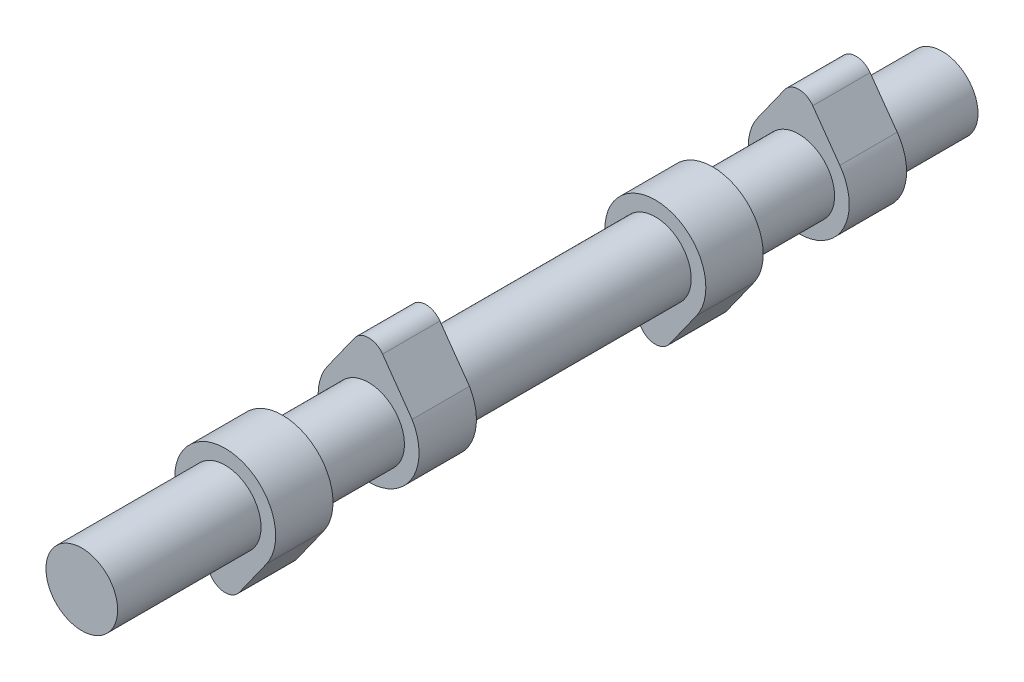
SolidWorks part; units mm, degrees
ref_plane "Front Plane" through (0, 0, 0) normal (0, 0, 1) x (1, 0, 0)
ref_plane "Top Plane" through (0, 0, 0) normal (0, 1, 0) x (1, 0, 0)
ref_plane "Right Plane" through (0, 0, 0) normal (1, 0, 0) x (0, 0, -1)
sketch "Sketch1" plane through (0, 0, 0) normal (0, 0, 1) x (1, 0, 0)
  circle A0 centre (0, 0) radius 6.25
  dimension "D1" = 12.5
extrude "Boss-Extrude1" add sketch "Sketch1" along normal blind 125
ref_plane "Plane1" through (0, 0, 15) normal (0, 0, -1) x (-1, 0, 0)
sketch "Sketch3" plane through (0, 0, 15) normal (0, 0, -1) x (-1, 0, 0)
  line L1 (-2.4438, 11.74) -> (-7.1686, 5.104)
  line L2 (2.4438, 11.74) -> (7.1686, 5.104)
  circle A0 centre (0, 0) radius 6.25
  arc A1 (-7.1686, 5.104) -> (7.1686, 5.104) centre (0, 0) ccw
  arc A2 (2.4438, 11.74) -> (-2.4438, 11.74) centre (0, 10) ccw
extrude "Boss-Extrude2" add sketch "Sketch3" against normal blind 10
ref_plane "Plane2" through (0, 0, 40) normal (0, 0, -1) x (-1, 0, 0)
ref_plane "Plane3" through (0, 0, 15) normal (0, 0, -1) x (-1, 0, 0)
sketch "Sketch6" plane through (0, 0, 40) normal (0, 0, -1) x (-1, 0, 0)
  line L1 (-2.4438, -11.74) -> (-7.1686, -5.104)
  line L2 (2.4438, -11.74) -> (7.1686, -5.104)
  circle A0 centre (0, 0) radius 6.25
  arc A1 (7.1686, -5.104) -> (-7.1686, -5.104) centre (0, 0) ccw
  arc A2 (-2.4438, -11.74) -> (2.4438, -11.74) centre (0, -10) ccw
extrude "Boss-Extrude3" add sketch "Sketch6" against normal blind 10
ref_plane "Plane4" through (0, 0, 90) normal (0, 0, -1) x (-1, 0, 0)
sketch "Sketch7" plane through (0, 0, 40) normal (0, 0, -1) x (-1, 0, 0)
  line L2 (2.4438, -11.74) -> (7.1686, -5.104)
  line L3 (-7.1686, -5.104) -> (-2.4438, -11.74)
  line L4 (2.4438, -11.74) -> (7.1686, -5.104)
  line L5 (-7.1686, -5.104) -> (-2.4438, -11.74)
  arc A2 (-2.4438, -11.74) -> (2.4438, -11.74) centre (0, -10) ccw
  arc A3 (7.1686, -5.104) -> (-7.1686, -5.104) centre (0, 0) ccw
  arc A4 (-2.4438, -11.74) -> (2.4438, -11.74) centre (0, -10) ccw
  arc A5 (7.1686, -5.104) -> (-7.1686, -5.104) centre (0, 0) ccw
  dimension "D1" = 0
sketch "Sketch8" plane through (0, 0, 90) normal (0, 0, -1) x (-1, 0, 0)
  line L0 (-2.4438, 11.74) -> (-7.5875, 4.4576)
  line L1 (2.4438, 11.74) -> (7.1686, 5.104)
  arc A0 (-6.7378, 5.6605) -> (7.1686, 5.104) centre (0, 0) ccw
  circle A1 centre (0, 0) radius 6.25
  arc A2 (2.4438, 11.74) -> (-2.4569, 11.7215) centre (0, 10) ccw
extrude "Boss-Extrude4" add sketch "Sketch8" against normal blind 10 contours L1 A2 L0 A0 A1
ref_plane "Plane5" through (0, 0, 115) normal (0, 0, -1) x (-1, 0, 0)
sketch "Sketch9" plane through (0, 0, 115) normal (0, 0, -1) x (-1, 0, 0)
  line L0 (2.4438, -11.74) -> (7.1686, -5.104)
  line L1 (-7.1686, -5.104) -> (-2.4438, -11.74)
  circle A1 centre (0, 0) radius 6.25
  arc A2 (-2.4438, -11.74) -> (2.4438, -11.74) centre (0, -10) ccw
  arc A3 (7.1686, -5.104) -> (-7.1686, -5.104) centre (0, 0) ccw
extrude "Boss-Extrude6" add sketch "Sketch9" against normal blind 10
sketch "Sketch14" plane through (0, 0, 125) normal (0, 0, 1) x (1, 0, 0)
  circle A0 centre (0, 0) radius 6.25
  dimension "D1" = 12.5
extrude "Boss-Extrude7" add sketch "Sketch14" along normal blind 25
